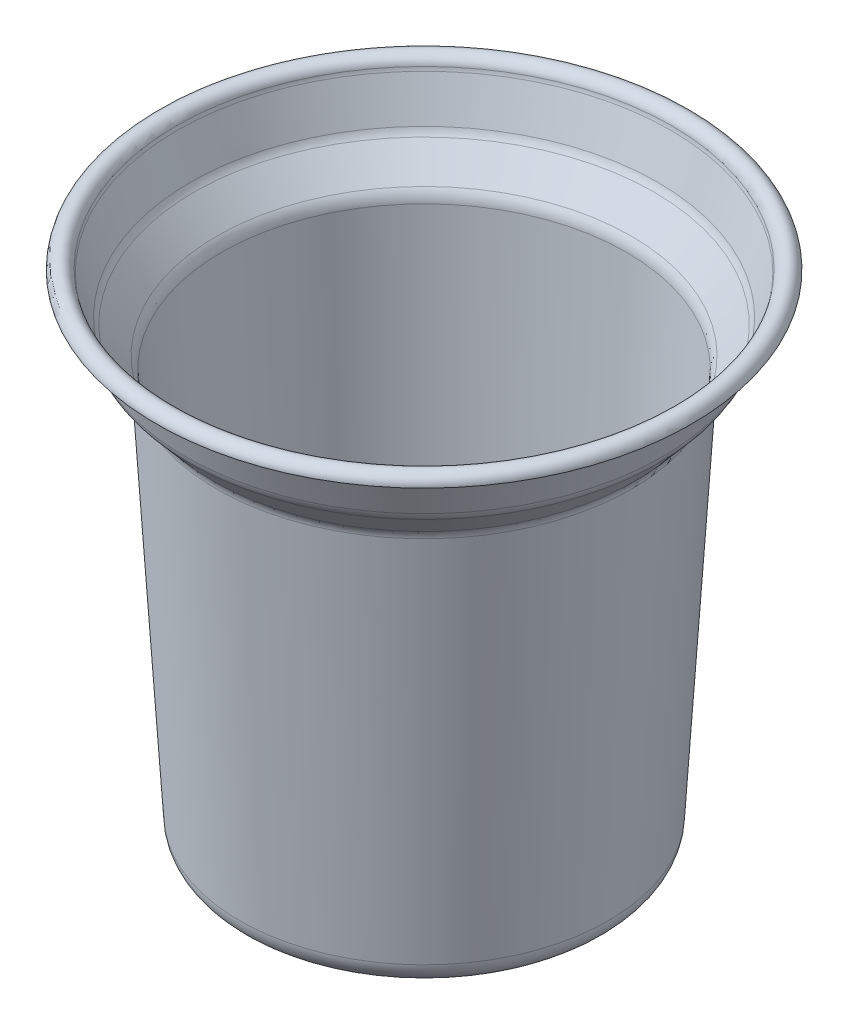
SolidWorks part; units mm, degrees
material "A286 Iron Base Superalloy"
ref_plane "Front Plane" through (0, 0, 0) normal (0, 0, 1) x (1, 0, 0)
ref_plane "Top Plane" through (0, 0, 0) normal (0, 1, 0) x (1, 0, 0)
ref_plane "Right Plane" through (0, 0, 0) normal (1, 0, 0) x (0, 0, -1)
sketch "Sketch1" plane through (0, 0, 0) normal (0, 0, 1) x (1, 0, 0)
  line L0 (0, 0) -> (32.2337, 0)
  line L1 (36.2265, 3.7595) -> (40.9192, 81.6581)
  line L2 (41.8749, 84.0207) -> (46.4901, 89.4051)
  line L3 (47.2478, 90.7433) -> (49.8506, 98.5517)
  line L4 (0, -6.7274) -> (0, 90.0251) construction
  arc A0 (50.0186, 99.2722) -> (54, 99) centre (52, 99) cw
  arc A1 (49.8506, 98.5517) -> (50.0186, 99.2722) centre (46.0558, 99.8166) ccw
  arc A2 (46.4901, 89.4051) -> (47.2478, 90.7433) centre (43.453, 92.0083) ccw
  arc A3 (40.9192, 81.6581) -> (41.8749, 84.0207) centre (44.9119, 81.4175) cw
  arc A4 (32.2337, 0) -> (36.2265, 3.7595) centre (32.2337, 4) ccw
  point P16 (50, 99)
  point P19 (47, 90)
  point P22 (41, 83)
  point P25 (36, 0)
  dimension "D5" = 9
  dimension "D4" = 2
  dimension "D9" = 4
  dimension "D1" = 36
  dimension "D2" = 83
  dimension "D3" = 7
  dimension "D6" = 41
  dimension "D7" = 47
  dimension "D8" = 50
revolve "Revolve-Thin1" add sketch "Sketch1" angle 360 about L4
